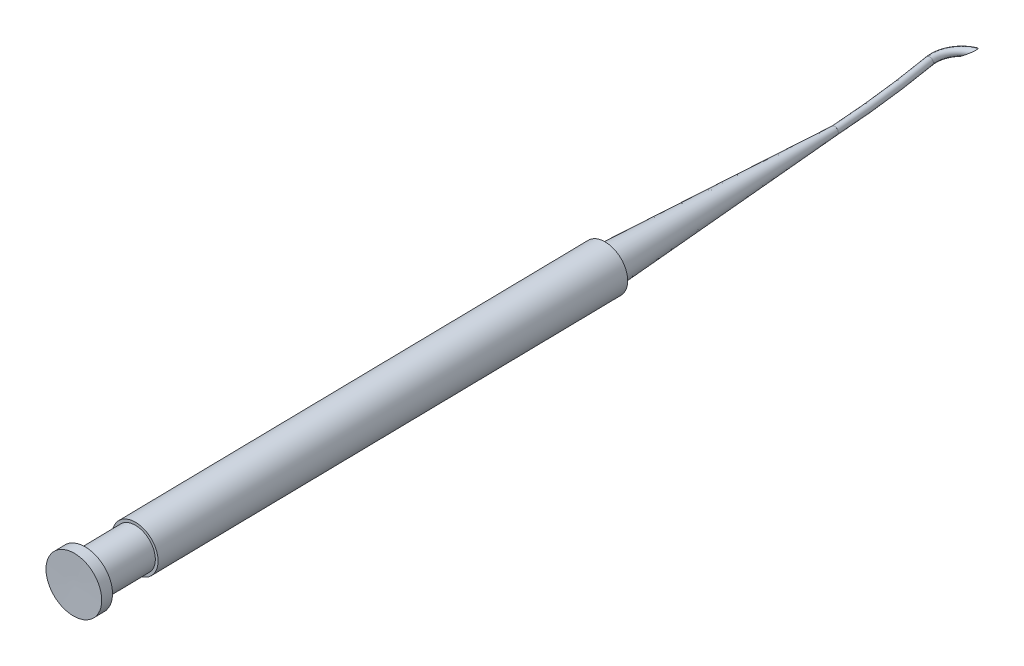
SolidWorks part; units mm, degrees
ref_plane "Front Plane" through (0, 0, 0) normal (0, 0, 1) x (1, 0, 0)
ref_plane "Top Plane" through (0, 0, 0) normal (0, 1, 0) x (1, 0, 0)
ref_plane "Right Plane" through (0, 0, 0) normal (1, 0, 0) x (0, 0, -1)
sketch "linear trace" plane through (0, 0, 0) normal (0, 1, 0) x (1, 0, 0)
  line L0 (160, 640) -> (800, 640) construction
  line L1 (24.3375, 49.7918) -> (24.8861, 17.0058)
  line L2 (24.8861, 17.0058) -> (26.1074, -55.9837)
  line L3 (25.1593, 43.7784) -> (27.244, 18.0728) construction
  line L4 (23.9729, 43.7784) -> (22.4925, 18.0728) construction
  line L5 (22.4925, 18.0728) -> (27.244, 18.0728) construction
  arc A0 (24.9673, 68.7253) -> (22.583, 64.5017) centre (26.347, 65.1616) ccw
  arc A1 (22.583, 64.5017) -> (24.3375, 49.7918) centre (-110.4989, 41.1687) cw
  point P13 (24.8682, 18.0728)
sketch "Sketch2" plane through (0, 0, 0) normal (0, 1, 0) x (1, 0, 0)
  line L0 (24.8861, 17.0058) -> (26.1074, -55.9837) construction
  line L1 (24.3375, 49.7918) -> (24.8861, 17.0058) construction
  line L2 (24.8861, 17.0058) -> (26.1074, -55.9837)
  line L3 (24.3375, 49.7918) -> (24.8861, 17.0058)
  line L4 (24.3375, 49.7918) -> (24.8375, 49.7918)
  line L5 (24.8375, 49.7918) -> (27.1636, 17.8476)
  line L6 (27.9725, 17.8476) -> (29.0656, -47.4848)
  line L7 (28.6906, -47.4848) -> (28.8077, -54.4839)
  line L8 (28.8077, -54.4839) -> (29.8329, -54.4839)
  line L9 (29.8329, -54.4839) -> (29.8579, -55.9837)
  line L10 (29.8579, -55.9837) -> (26.1074, -55.9837)
  line L11 (28.6906, -47.4848) -> (29.0656, -47.4848)
  line L12 (27.1636, 17.8476) -> (27.9725, 17.8476)
  dimension "D1" = 3.1
  dimension "D2" = 72.9996
  dimension "D3" = 2.725
  dimension "D4" = 3.75
  dimension "D5" = 1.5
  dimension "D6" = 7
  dimension "D7" = 0.5
revolve "Revolve4" add sketch "Sketch2" angle 360 about L2
sketch "Sketch4" plane through (0, 0, 0) normal (0, 1, 0) x (1, 0, 0)
  line L0 (23.8378, 49.775) -> (24.8375, 49.7918) construction
  line L1 (23.8378, 49.775) -> (24.8375, 49.7918) construction
  arc A0 (24.3375, 49.7918) -> (22.583, 64.5017) centre (-110.4989, 41.1687) ccw construction
  arc A1 (24.9673, 68.7253) -> (22.583, 64.5017) centre (26.347, 65.1616) ccw construction
  arc A2 (24.3375, 49.7918) -> (22.583, 64.5017) centre (-110.4989, 41.1687) ccw
  arc A3 (24.9673, 68.7253) -> (22.583, 64.5017) centre (26.347, 65.1616) ccw
ref_plane "Plane1" through (0, 0, -49.7918) normal (0, 0, -1) x (-1, 0, 0)
sketch "Sketch5" plane through (0, 0, -49.7918) normal (0, 0, -1) x (-1, 0, 0)
  circle A0 centre (-24.3376, 0) radius 0.15
  ellipse E0 centre (-24.3376, 0) end of major axis (-24.3376, -0.4999) minor radius 0.4999 construction
  ellipse E1 centre (-24.3376, 0) end of major axis (-24.3376, -0.4999) minor radius 0.4999
  dimension "D1" = 0.3
sweep "Sweep1" add profiles "Sketch5" path "Sketch4"
sketch "Sketch6" plane through (42.4234, 0, -13.3807) normal (0.9537, 0, -0.3008) x (-0.3008, 0, -0.9537)
  line L1 (58.6518, 0.4999) -> (56.562, 0.4999) construction
  ellipse E2 centre (58.0321, 0) end of major axis (58.0321, -0.4999) minor radius 0.4999 construction
ref_plane "Plane3" through (10.3994, -18.887, -3.2801) normal (-0.4768, 0.866, 0.1504) x (0.3008, 0, 0.9537)
sketch "Sketch7" plane through (10.3994, -18.887, -3.2801) normal (-0.4768, 0.866, 0.1504) x (0.3008, 0, 0.9537)
  line L1 (-57.1598, 40.0311) -> (-59.5041, 40.0311)
  line L2 (-57.1598, 40.0311) -> (-57.1598, 34.5665)
  line L3 (-57.1598, 34.5665) -> (-59.5041, 34.5665)
  line L4 (-59.5041, 40.0311) -> (-59.5041, 34.5665)
extrude "Cut-Extrude1" cut sketch "Sketch7" against normal blind 10
equation "\"D1@Sketch5\"=1-0.7"
